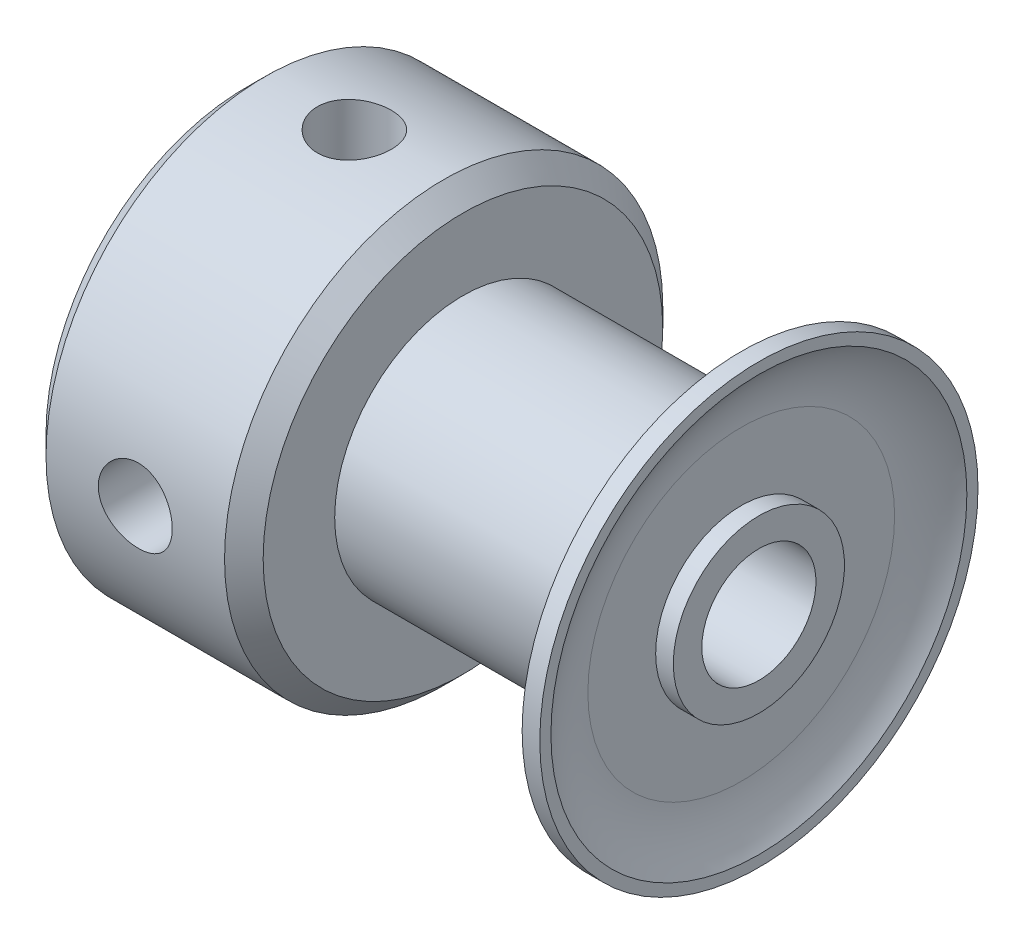
SolidWorks part; units mm, degrees
ref_plane "Front Plane" through (0, 0, 0) normal (0, 0, 1) x (1, 0, 0)
ref_plane "Top Plane" through (0, 0, 0) normal (0, 1, 0) x (1, 0, 0)
ref_plane "Right Plane" through (0, 0, 0) normal (1, 0, 0) x (0, 0, -1)
sketch "Sketch2" plane through (0, 0, 0) normal (0, 0, 1) x (1, 0, 0)
  line L1 (-7.1374, 0) -> (7.1374, 0) construction
  line L2 (0, -1.094) -> (0, 4.8952) construction
  line L3 (-7.1374, 1.5875) -> (7.1374, 1.5875)
  line L4 (-7.1374, 1.5875) -> (-7.1374, 2.3812)
  line L5 (-7.1374, 2.3812) -> (-1.096, 2.3813)
  line L6 (-1.096, 2.3813) -> (-1.096, 3.5687)
  line L7 (-1.096, 3.5687) -> (6.0668, 3.5687)
  line L8 (6.0668, 3.5687) -> (6.0668, 2.3813)
  line L9 (6.0668, 2.3813) -> (7.1374, 2.3812)
  line L10 (7.1374, 2.3812) -> (7.1374, 1.5875)
  dimension "D3" = 1.0706
  dimension "D4" = 4.7625
  dimension "Dimension [E]" = 14.2748
  dimension "Bore [A]" = 3.175
  dimension "Width [DD]" = 7.1628
  dimension "Outside Diameter [B]" = 7.1374
revolve "Base Body" add sketch "Sketch2" angle 360 about L1
sketch "Sketch3" plane through (0, 0, 0) normal (0, 1, 0) x (1, 0, 0)
  line L0 (-1.096, 2.3812) -> (-7.1374, 2.3812) construction
  line L1 (-1.096, 2.3812) -> (-7.1374, 2.3812)
  line L2 (-1.096, 2.3812) -> (-1.096, 5.5588)
  line L3 (-1.6332, 6.096) -> (-6.6002, 6.096)
  line L4 (-7.1374, 2.3812) -> (-7.1374, 5.5588)
  line L5 (-1.096, 3.5687) -> (-1.096, -3.5687) construction
  line L6 (-7.1374, 5.5588) -> (-6.6002, 6.096)
  line L7 (0, 0) -> (-7.1374, 0) construction
  line L8 (-7.1374, 2.3812) -> (-7.1374, -2.3812) construction
  line L9 (-4.1167, 2.3812) -> (-4.1167, 6.096) construction
  line L10 (-1.096, 5.5588) -> (-1.6332, 6.096)
  line L11 (-7.1374, 5.5588) -> (-7.1374, 6.096) construction
  line L12 (-7.1374, 6.096) -> (-6.6002, 6.096) construction
  dimension "Hub Diameter [F]" = 12.192
  dimension "D2" = 0.5372
revolve "Hub" add sketch "Sketch3" angle 360 about L7
sketch "Sketch4" plane through (0, 0, 0) normal (0, 1, 0) x (1, 0, 0)
  line L0 (6.0668, 2.3812) -> (6.0668, 4.2672)
  line L3 (0, 0) -> (7.0313, 0) construction
  line L4 (6.0668, 2.3812) -> (6.6464, 2.3812)
  line L5 (6.6464, 2.3812) -> (6.6464, 4.2672)
  line L6 (6.6464, 6.096) -> (7.1374, 5.7863) construction
  line L7 (6.6464, 6.096) -> (7.1374, 6.096)
  line L8 (7.1374, 6.096) -> (7.1374, 5.7863)
  arc A0 (6.0668, 4.2672) -> (6.6464, 6.096) centre (9.2418, 4.2672) cw
  arc A1 (6.6464, 4.2672) -> (7.1374, 5.7863) centre (9.2418, 4.2672) cw
  dimension "D2" = 3.175
  dimension "D1" = 4.2672
  dimension "Diameter [CC]" = 12.192
revolve "Flange" add sketch "Sketch4" angle 360 about L3
sketch "Sketch5" plane through (0, 0, 0) normal (0, 1, 0) x (1, 0, 0)
  line L0 (-4.1167, 6.096) -> (-4.1167, -6.096) construction
  line L1 (-6.6002, -6.096) -> (-1.6332, -6.096) construction
  line L2 (-1.6332, 6.096) -> (-6.6002, 6.096) construction
  circle A0 centre (-4.1167, 0) radius 1.0287
  dimension "Diameter [DI]" = 2.0574
extrude "Set Screws" cut sketch "Sketch5" along normal blind 10
cosmetic thread "Cosmetic Thread2" parameters "D2"=2.1603
pattern_circular "CirPattern1" count 2 over 90 about axis through (-7.1374, 0, 0) along (1, 0, 0) of "Set Screws"
cosmetic thread "Cosmetic Thread1" parameters "D2"=2.1603
equation "\"D4@Sketch2\" = \"Bore [A]@Sketch2\"*1.5"
equation "\"D3@Sketch2\" = \"Dimension [E]@Sketch2\"*.075"
equation "\"D2@Sketch3\" = \"Width [DD]@Sketch2\"*.075"
equation "\"D1@Sketch4\" = \"Diameter [CC]@Sketch4\"*.35"
equation "\"D2@Cosmetic Thread2\" = \"Diameter [DI]@Sketch5\"*1.05"
equation "\"D2@Cosmetic Thread1\" = \"D2@Cosmetic Thread2\""
